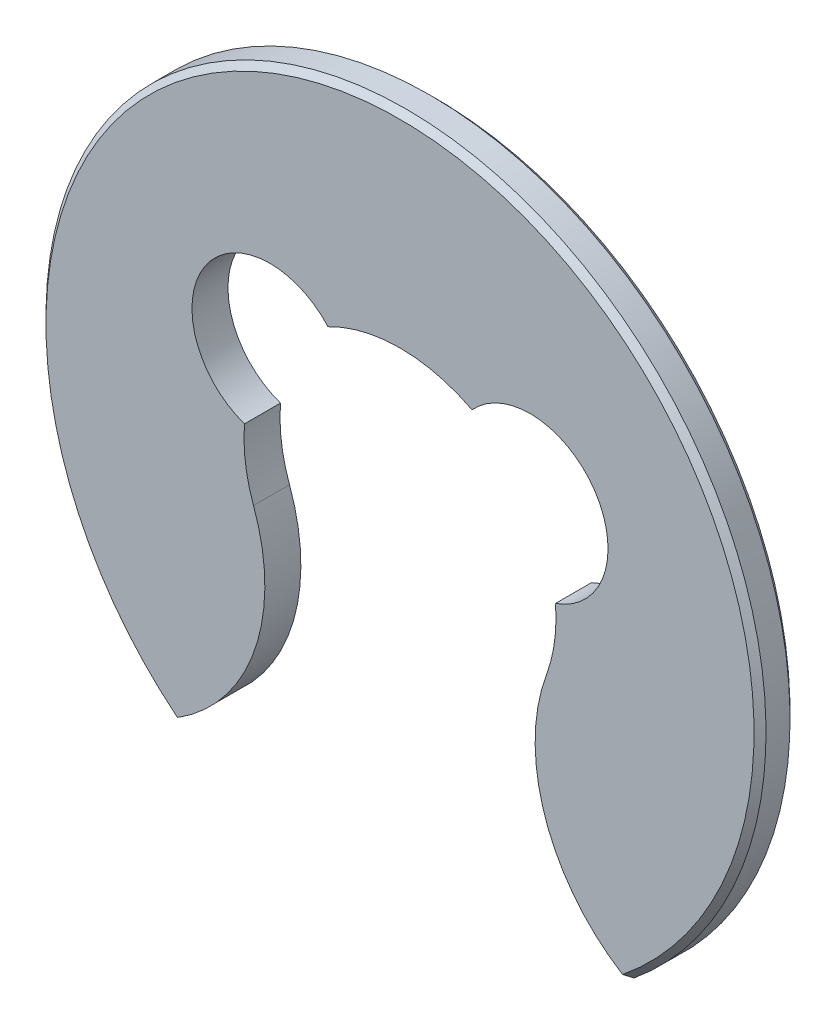
SolidWorks part; units mm, degrees
ref_plane "前视基准面" through (0, 0, 0) normal (0, 0, 1) x (1, 0, 0)
ref_plane "上视基准面" through (0, 0, 0) normal (0, 1, 0) x (1, 0, 0)
ref_plane "右视基准面" through (0, 0, 0) normal (1, 0, 0) x (0, 0, -1)
sketch "草图1" plane through (0, 0, 0) normal (0, 0, 1) x (1, 0, 0)
  line L0 (0, 2.0518) -> (0, -3.5323) construction
  arc A0 (-1.2958, 0.1043) -> (-1.2206, -0.4473) centre (0, 0) ccw
  arc A1 (1.9, -2.3216) -> (-1.9, -2.3216) centre (0, 0) ccw
  arc A2 (-0.6, 1.1532) -> (-1.2958, 0.1043) centre (-1.0833, 0.7186) ccw
  arc A3 (1.2958, 0.1043) -> (0.6, 1.1532) centre (1.0833, 0.7186) ccw
  arc A4 (-1.2206, -0.4473) -> (-1.9, -2.3216) centre (-2.6753, -0.9803) cw
  arc A5 (1.2206, -0.4473) -> (1.9, -2.3216) centre (2.6753, -0.9803) ccw
  arc A6 (0.6, 1.1532) -> (-0.6, 1.1532) centre (0, 0) ccw
  arc A7 (1.2206, -0.4473) -> (1.2958, 0.1043) centre (0, 0) ccw
  dimension "D1" = 2.6
  dimension "D2" = 6
  dimension "D6" = 3.8
extrude "凸台-拉伸1" add sketch "草图1" along normal blind 0.3
chamfer "倒角1" distance 0.05 angle 45 2 edges at (0, 3, 0.3) (0, 3, 0)
